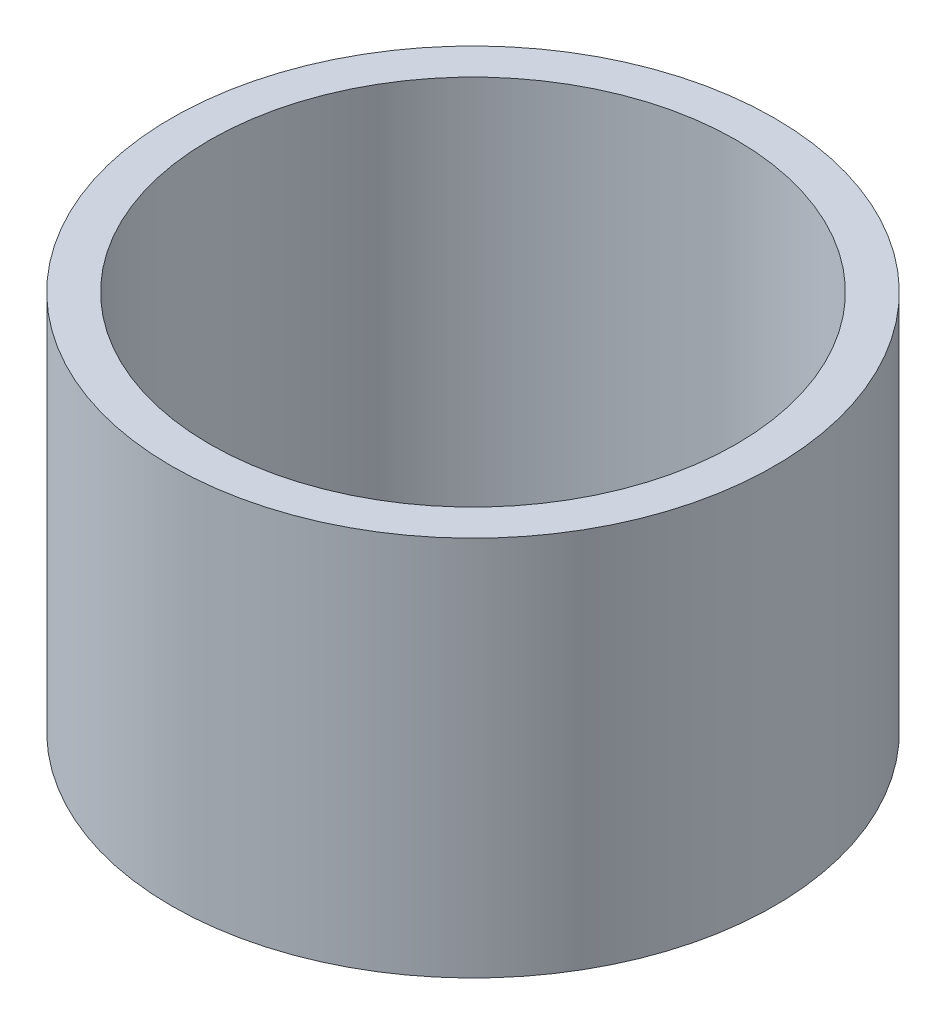
SolidWorks part; units mm, degrees
material "Epoxy, Unfilled"
ref_plane "Front Plane" through (0, 0, 0) normal (0, 0, 1) x (1, 0, 0)
ref_plane "Top Plane" through (0, 0, 0) normal (0, 1, 0) x (1, 0, 0)
ref_plane "Right Plane" through (0, 0, 0) normal (1, 0, 0) x (0, 0, -1)
sketch "Sketch1" plane through (0, 0, 0) normal (0, 1, 0) x (1, 0, 0)
  circle A0 centre (0, 0) radius 50.2539
  circle A1 centre (0, 0) radius 43.9039
extrude "Boss-Extrude1" add sketch "Sketch1" along normal blind 63.5
